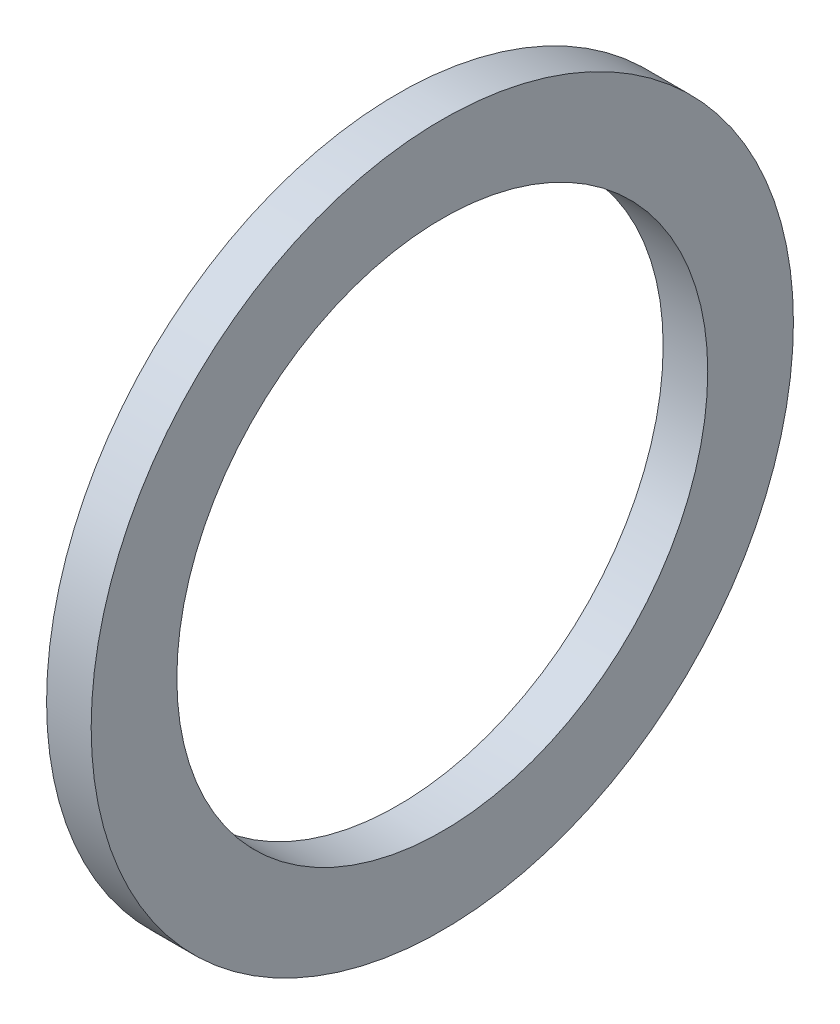
SolidWorks part; units mm, degrees
ref_plane "Front Plane" through (0, 0, 0) normal (0, 0, 1) x (1, 0, 0)
ref_plane "Top Plane" through (0, 0, 0) normal (0, 1, 0) x (1, 0, 0)
ref_plane "Right Plane" through (0, 0, 0) normal (1, 0, 0) x (0, 0, -1)
sketch "Sketch1" plane through (0, 0, 0) normal (1, 0, 0) x (0, 0, -1)
  circle A0 centre (0, 0) radius 18.9
  circle A1 centre (0, 0) radius 25
  dimension "D1" = 50
  dimension "D2" = 37.8
extrude "Boss-Extrude1" add sketch "Sketch1" along normal blind 3.175
